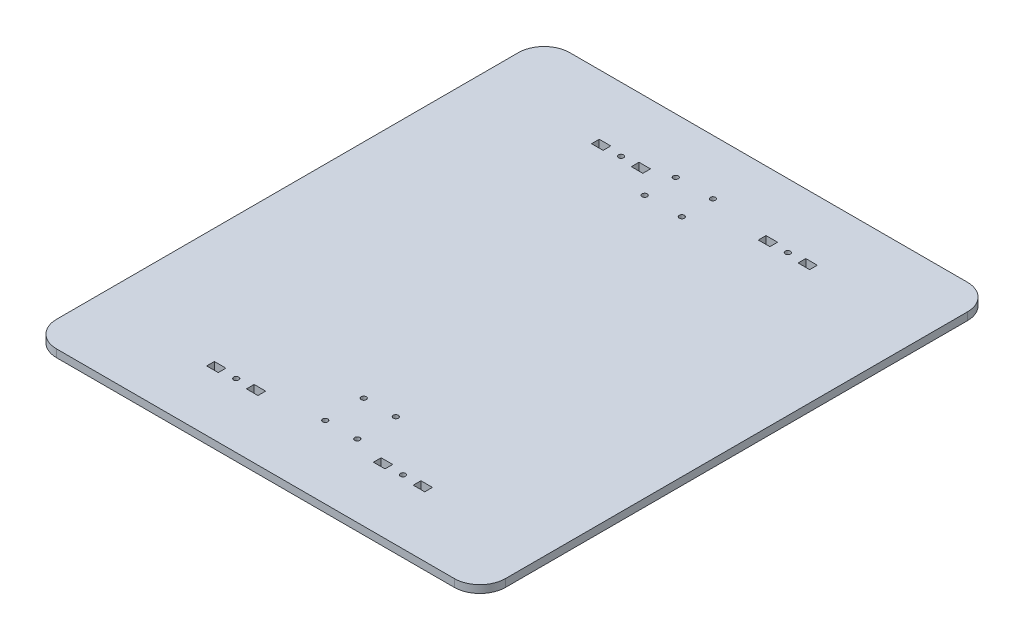
SolidWorks part; units mm, degrees
ref_plane "Front Plane" through (0, 0, 0) normal (0, 0, 1) x (1, 0, 0)
ref_plane "Top Plane" through (0, 0, 0) normal (0, 1, 0) x (1, 0, 0)
ref_plane "Right Plane" through (0, 0, 0) normal (1, 0, 0) x (0, 0, -1)
sketch "Sketch1" plane through (0, 0, 0) normal (0, 1, 0) x (1, 0, 0)
  line L1 (-155, -200) -> (155, -200)
  line L2 (-175, -180) -> (-175, 180)
  line L3 (-155, 200) -> (155, 200)
  line L4 (175, -180) -> (175, 180)
  line L5 (-175, -200) -> (175, 200) construction
  line L6 (-175, 200) -> (175, -200) construction
  arc A0 (155, 200) -> (175, 180) centre (155, 180) cw
  arc A1 (175, -180) -> (155, -200) centre (155, -180) cw
  arc A2 (-155, -200) -> (-175, -180) centre (-155, -180) cw
  arc A3 (-175, 180) -> (-155, 200) centre (-155, 180) cw
  point P0 (0, 0)
  point P6 (0, 0)
  dimension "D5" = 20
  dimension "D1" = 400
  dimension "D2" = 350
extrude "Boss-Extrude1" add sketch "Sketch1" along normal blind 6
sketch "Sketch2" plane through (0, 6, 0) normal (0, 1, 0) x (1, 0, 0)
  line L0 (0, 0) -> (0, -200) construction
  line L1 (-155, -200) -> (155, -200) construction
  line L3 (-2, -113.5596) -> (23, -113.5596) construction
  line L4 (-2, -113.5596) -> (-2, -143.5596) construction
  line L5 (-2, -143.5596) -> (23, -143.5596) construction
  line L6 (23, -113.5596) -> (23, -143.5596) construction
  circle A0 centre (-2, -113.5596) radius 2
  circle A1 centre (23, -113.5596) radius 2
  circle A2 centre (23, -143.5596) radius 2
  circle A3 centre (-2, -143.5596) radius 2
  dimension "D3" = 4
  dimension "D1" = 25
  dimension "D2" = 30
  dimension "D4" = 2
extrude "Cut-Extrude1" cut sketch "Sketch2" against normal blind 10
sketch "Sketch3" plane through (0, 6, 0) normal (0, 1, 0) x (1, 0, 0)
  line L0 (-45, 147) -> (-54, 147)
  line L1 (-65, -150) -> (65, -150) construction
  line L2 (-65, -150) -> (-65, 150) construction
  line L3 (-65, 150) -> (65, 150) construction
  line L4 (65, -150) -> (65, 150) construction
  line L5 (-65, -150) -> (65, 150) construction
  line L6 (-65, 150) -> (65, -150) construction
  line L7 (-65, 150) -> (-80.5, 150) construction
  line L8 (-54, 147) -> (-54, 153)
  line L9 (-85, 147) -> (-76, 147)
  line L10 (-85, 147) -> (-85, 153)
  line L11 (-85, 153) -> (-76, 153)
  line L12 (-76, 147) -> (-76, 153)
  line L13 (-85, 147) -> (-76, 153) construction
  line L14 (-85, 153) -> (-76, 147) construction
  line L15 (-45, 153) -> (-54, 153)
  line L16 (-45, 147) -> (-45, 153)
  line L17 (0, 0) -> (0, 168.6208) construction
  line L18 (45, 153) -> (54, 153)
  line L19 (45, 147) -> (45, 153)
  line L20 (45, 147) -> (54, 147)
  line L21 (54, 147) -> (54, 153)
  line L22 (85, 147) -> (76, 147)
  line L23 (76, 147) -> (76, 153)
  line L24 (85, 153) -> (76, 153)
  line L25 (85, 147) -> (85, 153)
  line L26 (0, 0) -> (80.6943, 0) construction
  line L27 (85, -153) -> (76, -153)
  line L28 (85, -147) -> (85, -153)
  line L29 (85, -147) -> (76, -147)
  line L30 (76, -147) -> (76, -153)
  line L31 (54, -147) -> (54, -153)
  line L32 (45, -147) -> (45, -153)
  line L33 (45, -147) -> (54, -147)
  line L34 (45, -153) -> (54, -153)
  line L35 (-45, -147) -> (-45, -153)
  line L36 (-54, -147) -> (-54, -153)
  line L37 (-45, -153) -> (-54, -153)
  line L38 (-45, -147) -> (-54, -147)
  line L39 (-76, -147) -> (-76, -153)
  line L40 (-85, -147) -> (-76, -147)
  line L41 (-85, -153) -> (-76, -153)
  line L42 (-85, -147) -> (-85, -153)
  circle A0 centre (-65, 150) radius 2
  circle A1 centre (65, 150) radius 2
  circle A4 centre (65, -150) radius 2
  circle A5 centre (-65, -150) radius 2
  point P0 (0, 0)
  dimension "D2" = 4
  dimension "D1" = 130
  dimension "D3" = 15.5
  dimension "D4" = 9
  dimension "D5" = 6
  dimension "D6" = 300
extrude "Cut-Extrude5" cut sketch "Sketch3" against normal blind 6
sketch "Sketch4" plane through (0, 6, 0) normal (0, 1, 0) x (1, 0, 0)
  line L1 (-29.4825, 132.89) -> (-0.5175, 132.89) construction
  line L2 (-29.4825, 132.89) -> (-29.4825, 157.11) construction
  line L3 (-29.4825, 157.11) -> (-0.5175, 157.11) construction
  line L4 (-0.5175, 132.89) -> (-0.5175, 157.11) construction
  line L5 (-29.4825, 132.89) -> (-0.5175, 157.11) construction
  line L6 (-29.4825, 157.11) -> (-0.5175, 132.89) construction
  circle A0 centre (-29.4825, 157.11) radius 2
  circle A1 centre (-0.5175, 157.11) radius 2
  circle A2 centre (-0.5175, 132.89) radius 2
  circle A3 centre (-29.4825, 132.89) radius 2
  point P0 (-15, 145)
  dimension "D5" = 4
  dimension "D1" = 15
  dimension "D2" = 145
  dimension "D3" = 28.965
  dimension "D4" = 24.22
extrude "Cut-Extrude6" cut sketch "Sketch4" against normal blind 24
